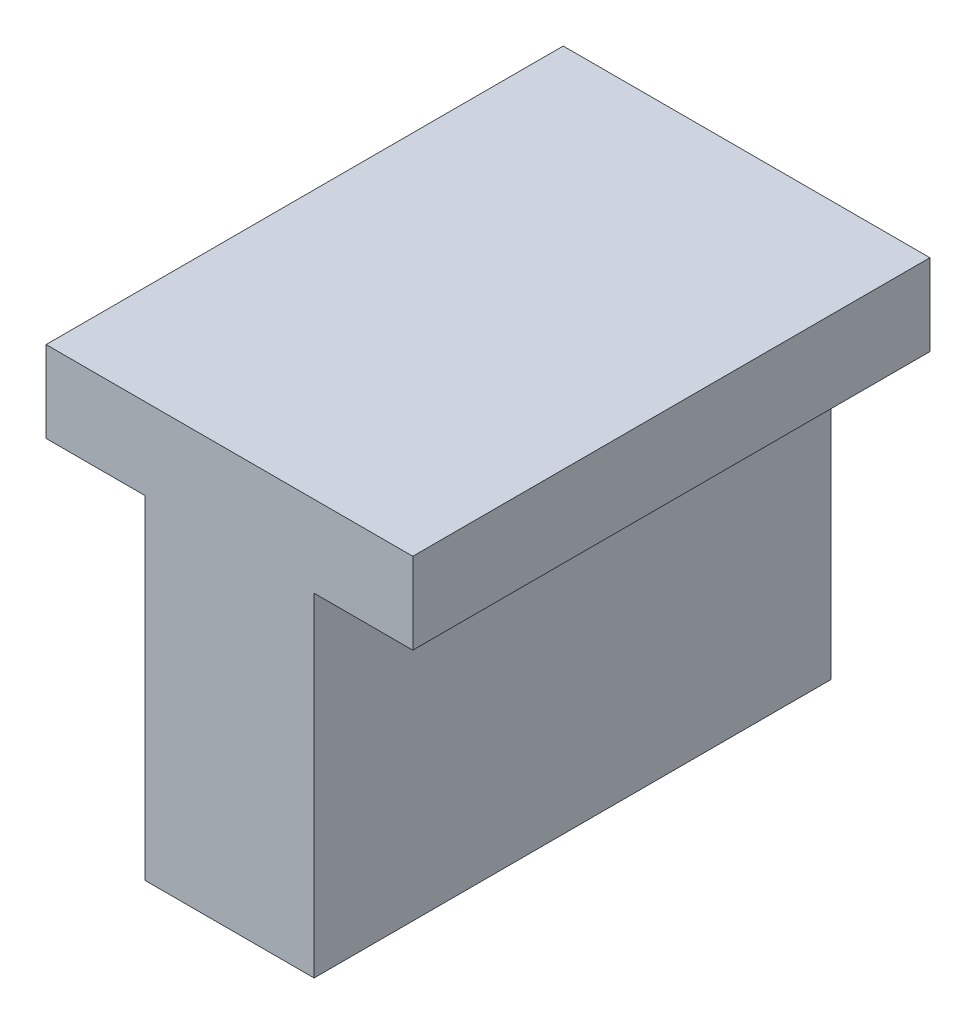
SolidWorks part; units mm, degrees
ref_plane "Front Plane" through (0, 0, 0) normal (0, 0, 1) x (1, 0, 0)
ref_plane "Top Plane" through (0, 0, 0) normal (0, 1, 0) x (1, 0, 0)
ref_plane "Right Plane" through (0, 0, 0) normal (1, 0, 0) x (0, 0, -1)
sketch "Sketch1" plane through (0, 0, 0) normal (0, 0, 1) x (1, 0, 0)
  line L0 (-40.1733, 24.5427) -> (-32.3733, 24.5427)
  line L1 (-40.1733, 24.5427) -> (-40.1733, 22.8127)
  line L2 (-32.3733, 24.5427) -> (-32.3733, 22.8127)
  line L3 (-40.1733, 22.8127) -> (-38.0733, 22.8127)
  line L4 (-32.3733, 22.8127) -> (-34.4733, 22.8127)
  line L5 (-38.0733, 22.8127) -> (-38.0733, 15.7237)
  line L6 (-34.4733, 22.8127) -> (-34.4733, 15.7237)
  line L7 (-38.0733, 15.7237) -> (-34.4733, 15.7237)
extrude "Boss-Extrude1" add sketch "Sketch1" along normal blind 11
